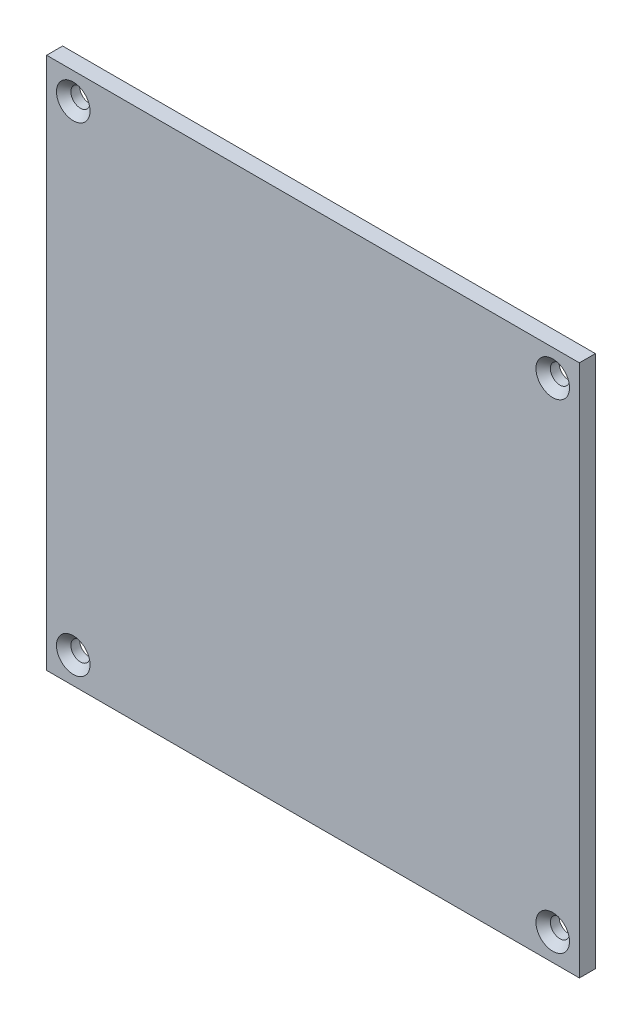
SolidWorks part; units mm, degrees
material "Perspex (TM) Plaque acrylique coulée"
ref_plane "Plan de face" through (0, 0, 0) normal (0, 0, 1) x (1, 0, 0)
ref_plane "Plan de dessus" through (0, 0, 0) normal (0, 1, 0) x (1, 0, 0)
ref_plane "Plan de droite" through (0, 0, 0) normal (1, 0, 0) x (0, 0, -1)
sketch "Esquisse1" plane through (0, 0, 0) normal (0, 0, 1) x (1, 0, 0)
  line L1 (0, 0) -> (100, 0)
  line L2 (0, 0) -> (0, 100)
  line L3 (0, 100) -> (100, 100)
  line L4 (100, 0) -> (100, 100)
  dimension "D1" = 100
  dimension "D2" = 100
extrude "Boss.-Extru.1" add sketch "Esquisse1" along normal blind 3
hole_wizard "Fraisage pour vis à tête fraisée M31" positions "Esquisse3D1" profile "Esquisse3" countersink size "M3" standard "ISO" end condition through all
sketch3d "Esquisse3D1"
  line L0 (100, 100, 3) -> (0, 100, 3) construction
  line L1 (0, 100, 3) -> (0, 0, 3) construction
  line L2 (100, 0, 3) -> (100, 100, 3) construction
  line L3 (0, 0, 3) -> (100, 0, 3) construction
  point P0 (5, 95, 3)
  point P2 (95, 95, 3)
  point P4 (95, 5, 3)
  point P6 (5, 5, 3)
  dimension "D1" = 5
  dimension "D2" = 5
  dimension "D3" = 5
  dimension "D4" = 5
  dimension "D5" = 5
  dimension "D6" = 5
  dimension "D7" = 5
  dimension "D8" = 5
sketch "Esquisse3" plane through (5, 95, 3) normal (1, 0, 0) x (0, -1, 0)
  line L0 (0, 0) -> (0, 3)
  line L1 (0, 3) -> (1.8, 3)
  line L2 (1.8, 3) -> (1.8, 1.35)
  line L3 (1.8, 1.35) -> (3.15, 0)
  line L5 (3.15, 0) -> (0, 0)
  line L6 (-1.8, 1.35) -> (-3.15, 0) construction
  line L11 (0, -6.35) -> (0, 107.95) construction
  dimension "Diamètre du perçage jusqu'au prochain" = 3.6
  dimension "Profondeur du perçage jusqu'au prochain" = 3
  dimension "Diamètre du fraisage entrant" = 6.3
  dimension "Angle du fraisage entrant" = 90
